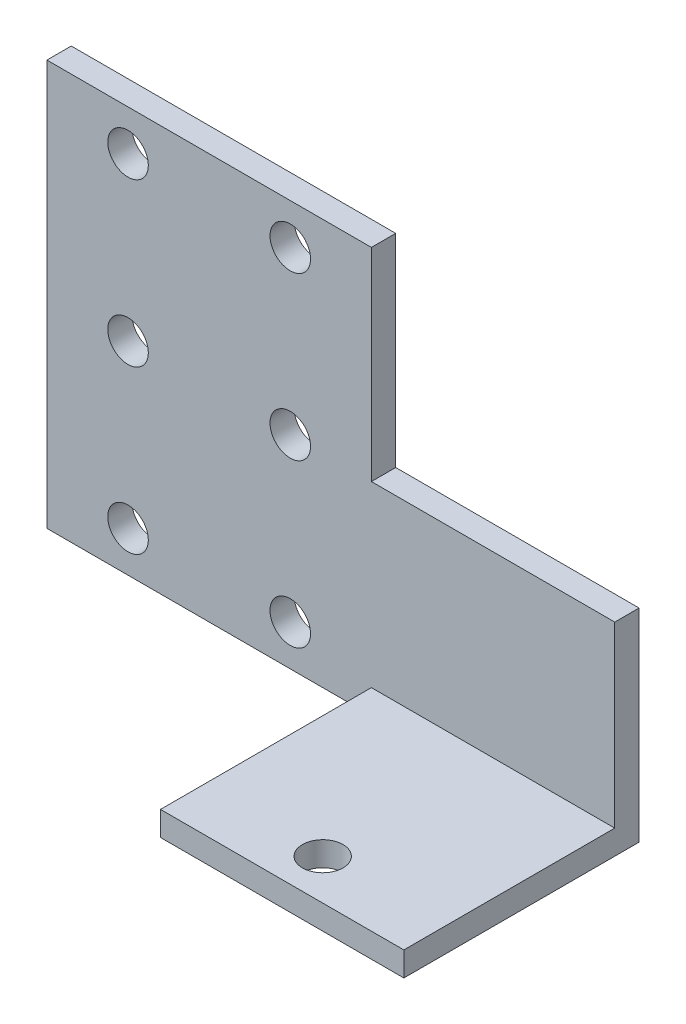
SolidWorks part; units mm, degrees
ref_plane "Front Plane" through (0, 0, 0) normal (0, 0, 1) x (1, 0, 0)
ref_plane "Top Plane" through (0, 0, 0) normal (0, 1, 0) x (1, 0, 0)
ref_plane "Right Plane" through (0, 0, 0) normal (1, 0, 0) x (0, 0, -1)
sketch "Sketch1" plane through (0, 0, 0) normal (0, 0, 1) x (1, 0, 0)
  line L0 (20, 50) -> (20, 0) construction
  line L1 (0, 0) -> (40, 0)
  line L2 (0, 0) -> (0, 50)
  line L3 (0, 50) -> (40, 50)
  line L4 (40, 0) -> (40, 50)
  line L5 (30, 45) -> (10, 45) construction
  line L6 (30, 45) -> (30, 25) construction
  line L7 (30, 45) -> (30, 50) construction
  line L8 (30, 5) -> (30, 0) construction
  circle A0 centre (30, 45) radius 2.5
  circle A1 centre (10, 45) radius 2.5
  circle A2 centre (10, 25) radius 2.5
  circle A3 centre (10, 5) radius 2.5
  circle A4 centre (30, 25) radius 2.5
  circle A5 centre (30, 5) radius 2.5
  point P9 (20, 45)
  point P24 (29.7165, 25)
  dimension "D7" = 5
  dimension "D1" = 50
  dimension "D2" = 40
  dimension "D5" = 20
  dimension "D6" = 5
  dimension "D3" = 2
  dimension "D4" = 3
extrude "Boss-Extrude1" add sketch "Sketch1" along normal blind 3
sketch "Sketch2" plane through (40, 0, 0) normal (1, 0, 0) x (0, 0, -1)
  line L0 (-3, 0) -> (-3, 50) construction
  line L1 (0, 0) -> (-29, 0)
  line L2 (0, 0) -> (0, 25)
  line L4 (-29, 0) -> (-29, 3)
  line L7 (-29, 3) -> (-3, 3)
  line L8 (-3, 25) -> (-3, 3)
  line L10 (-3, 25) -> (0, 25)
  line L11 (0, 0) -> (0, 50) construction
  point P1 (0, 25)
  dimension "D1" = 3
  dimension "D2" = 26
extrude "Boss-Extrude2" add sketch "Sketch2" along normal blind 30
sketch "Sketch4" plane through (0, 3, 0) normal (0, 1, 0) x (1, 0, 0)
  line L0 (70, -3) -> (40, -3) construction
  line L2 (55, -24) -> (55, -29) construction
  line L3 (70, -29) -> (40, -29) construction
  circle A0 centre (55, -24) radius 2.5
  point P0 (55, -19.6677)
  point P9 (55.5049, -17.8103)
  dimension "D1" = 5
  dimension "D2" = 21
extrude "Cut-Extrude2" cut sketch "Sketch4" against normal through all both
